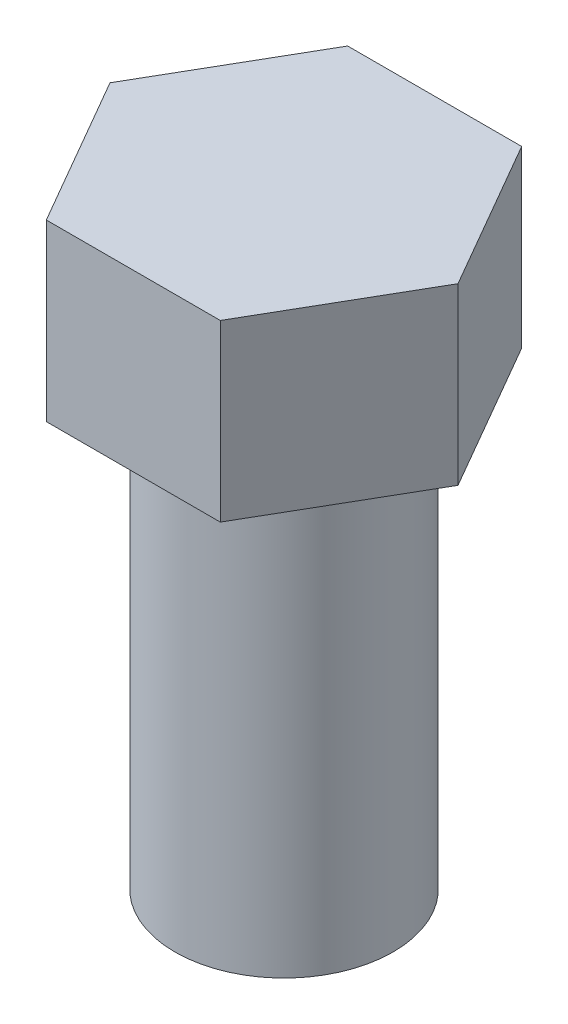
SolidWorks part; units mm, degrees
ref_plane "Front Plane" through (0, 0, 0) normal (0, 0, 1) x (1, 0, 0)
ref_plane "Top Plane" through (0, 0, 0) normal (0, 1, 0) x (1, 0, 0)
ref_plane "Right Plane" through (0, 0, 0) normal (1, 0, 0) x (0, 0, -1)
sketch "Sketch1" plane through (0, 0, 0) normal (0, 1, 0) x (1, 0, 0)
  circle A0 centre (0, 0) radius 63.5
extrude "Boss-Extrude1" add sketch "Sketch1" against normal blind 254
sketch "Sketch2" plane through (0, 0, 0) normal (0, 1, 0) x (1, 0, 0)
  line L0 (-50.6137, 87.6654) -> (50.6137, 87.6654)
  line L1 (50.6137, 87.6654) -> (101.2273, 0)
  line L2 (101.2273, 0) -> (50.6137, -87.6654)
  line L3 (50.6137, -87.6654) -> (-50.6137, -87.6654)
  line L4 (-50.6137, -87.6654) -> (-101.2273, 0)
  line L5 (-101.2273, 0) -> (-50.6137, 87.6654)
extrude "Boss-Extrude2" add sketch "Sketch2" along normal blind 101.6
